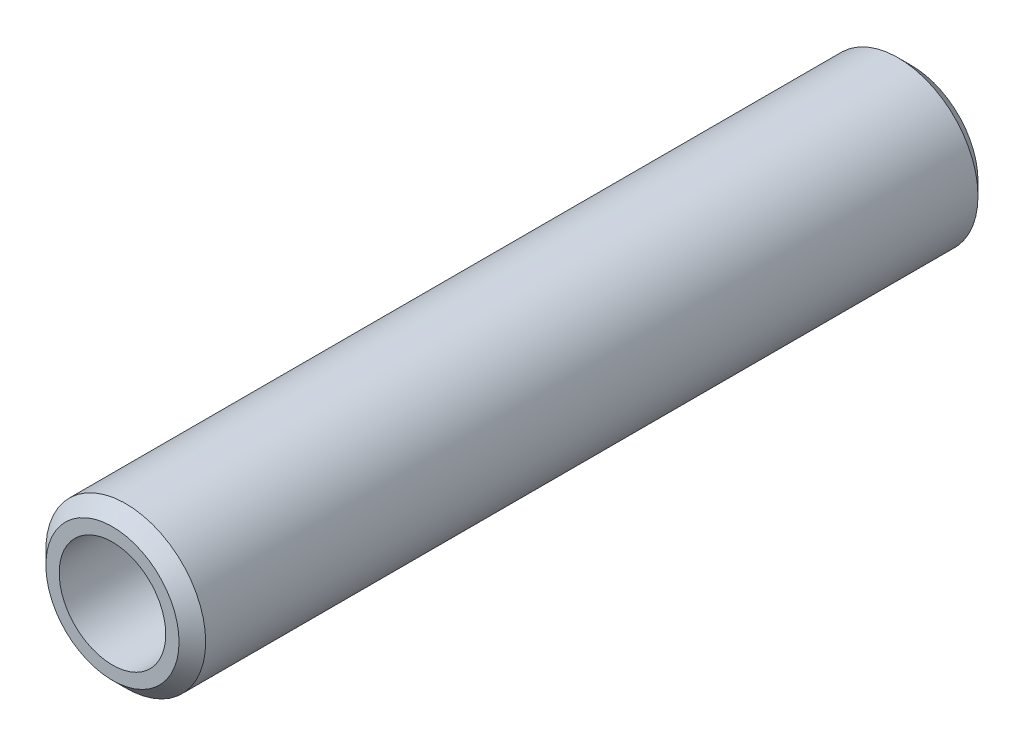
SolidWorks part; units mm, degrees
ref_plane "Ön Düzlem" through (0, 0, 0) normal (0, 0, 1) x (1, 0, 0)
ref_plane "Üst Düzlem" through (0, 0, 0) normal (0, 1, 0) x (1, 0, 0)
ref_plane "Sağ Düzlem" through (0, 0, 0) normal (1, 0, 0) x (0, 0, -1)
sketch "Çizim1" plane through (0, 0, 0) normal (0, 0, 1) x (1, 0, 0)
  circle A0 centre (-22.8344, 8.614) radius 3
  circle A1 centre (-22.8344, 8.614) radius 2
extrude "Yükseklik-Ekstrüzyon1" add sketch "Çizim1" along normal blind 30
chamfer "Pah1" distance 0.5 angle 45 2 edges at (-19.8344, 8.614, 30) (-19.8344, 8.614, 0)
